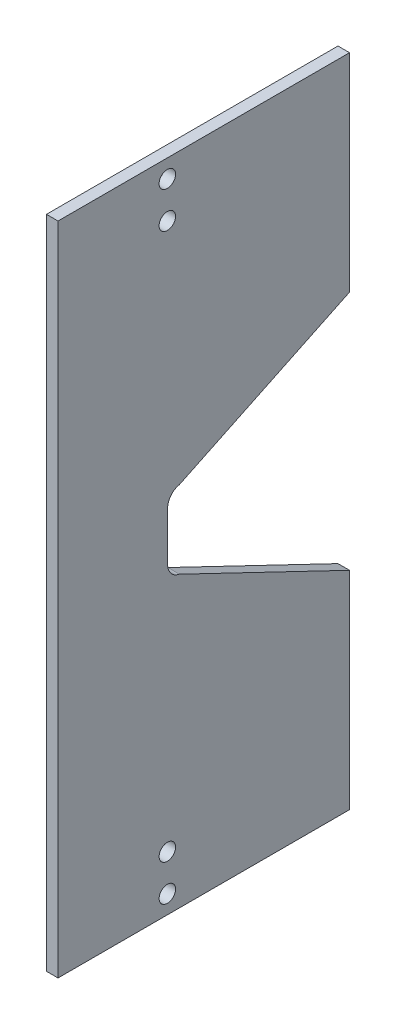
SolidWorks part; units mm, degrees
material "ABS"
ref_plane "前视基准面" through (0, 0, 0) normal (0, 0, 1) x (1, 0, 0)
ref_plane "上视基准面" through (0, 0, 0) normal (0, 1, 0) x (1, 0, 0)
ref_plane "右视基准面" through (0, 0, 0) normal (1, 0, 0) x (0, 0, -1)
ref_plane "基准面4" through (-0.7938, 0, 0) normal (-1, 0, 0) x (0, -1, 0)
sketch "草图1" plane through (-0.7938, 0, 0) normal (-1, 0, 0) x (0, -1, 0)
  line L1 (38.795, 5) -> (12.795, 5)
  line L2 (10.795, 3) -> (10.795, -13)
  line L5 (10.795, 3) -> (55.77, 3) construction
  line L6 (55.77, 3) -> (55.77, -5.0783) construction
  line L7 (55.77, 3) -> (55.77, 5) construction
  line L13 (38.795, 5) -> (72.745, 5)
  line L15 (100.745, 3) -> (100.745, -13)
  line L18 (72.745, 5) -> (98.745, 5)
  line L19 (55.77, 5) -> (55.77, -5.0783) construction
  line L20 (55.77, -5.0783) -> (55.77, -0.0391) construction
  line L21 (55.77, -0.0391) -> (65.77, -0.0391) construction
  line L22 (72.112, -14.1547) -> (62.1308, -0.0391) construction
  line L31 (12.795, -15) -> (47.795, -15)
  line L32 (55.77, -0.0391) -> (50.77, -0.0391)
  line L33 (55.77, -0.0391) -> (60.77, -0.0391)
  line L34 (98.745, -15) -> (63.745, -15)
  line L37 (50.77, -0.0391) -> (47.795, -15)
  line L38 (60.77, -0.0391) -> (63.745, -15)
  arc A2 (12.795, 5) -> (10.795, 3) centre (12.795, 3) ccw
  arc A3 (10.795, -13) -> (12.795, -15) centre (12.795, -13) ccw
  circle A5 centre (18.295, 0) radius 1.1303
  circle A6 centre (13.295, 0) radius 1.1303
  arc A12 (98.745, 5) -> (100.745, 3) centre (98.745, 3) cw
  arc A13 (100.745, -13) -> (98.745, -15) centre (98.745, -13) cw
  circle A14 centre (98.245, 0) radius 1.1303
  circle A15 centre (93.245, 0) radius 1.1303
extrude "凸台-拉伸1" add sketch "草图1" against normal blind 1.588
fillet "圆角1" radius 2 1 edges at (0.0002, -50.77, -0.0391)
fillet "圆角2" radius 2 1 edges at (0.0003, -47.795, -15)
fillet "圆角3" radius 2 1 edges at (0.0002, -60.77, -0.0391)
fillet "圆角4" radius 2 1 edges at (0.0003, -63.745, -15)
sketch "草图2" plane through (-0.7938, 0, 0) normal (-1, 0, 0) x (0, 0, 1)
  line L0 (5, -55.77) -> (15, -55.77) construction
  line L1 (5, -98.745) -> (5, -12.795) construction
  line L2 (15, -55.77) -> (15, -10.795) construction
  line L3 (15, -55.77) -> (15, -100.745) construction
  line L4 (15, -100.745) -> (3, -100.745) construction
  line L5 (3, -100.745) -> (3, -10.795) construction
  line L6 (3, -10.795) -> (15, -10.795) construction
  line L7 (3, -10.795) -> (15, -10.795)
  line L8 (15, -10.795) -> (15, -100.745)
  line L9 (15, -100.745) -> (3, -100.745)
  line L10 (3, -100.745) -> (3, -10.795)
  line L11 (-15, -29.4743) -> (-25, -29.4743) construction
  line L12 (-15, -12.795) -> (-15, -46.1535) construction
  line L13 (-25, -29.4743) -> (-25, -82.0657) construction
  line L14 (-25, -82.0657) -> (-25, -100.745) construction
  line L15 (-25, -100.745) -> (-13, -100.745) construction
  line L16 (-13, -100.745) -> (-13, -10.795) construction
  line L17 (-13, -10.795) -> (-25, -10.795) construction
  line L18 (-25, -10.795) -> (-25, -29.4743) construction
  line L19 (-1.6491, -50.4499) -> (-13.3901, -48.1151) construction
  line L20 (-13.3901, -48.1151) -> (-25, -45.8065) construction
  line L21 (-1.6491, -61.0901) -> (-13.3901, -63.4249) construction
  line L22 (-13.3901, -63.4249) -> (-25, -65.7335) construction
  line L23 (-25, -10.795) -> (-25, -45.8065)
  line L24 (-25, -45.8065) -> (-13.3901, -48.1151)
  line L26 (-13, -10.795) -> (-25, -10.795)
  line L27 (-13, -10.795) -> (-13.3901, -48.1151)
  line L28 (-13.3901, -63.4249) -> (-25, -65.7335)
  line L29 (-25, -65.7335) -> (-25, -100.745)
  line L30 (-25, -100.745) -> (-13, -100.745)
  line L31 (-13, -100.745) -> (-13.3901, -63.4249)
extrude "凸台-拉伸2" add sketch "草图2" against normal blind 1.588
sketch "草图5" plane through (0.7942, 0, 0) normal (1, 0, 0) x (0, 0, -1)
  line L0 (25, -10.795) -> (25, -45.8065) construction
  line L1 (25, -45.8065) -> (25, -28.3007) construction
  line L2 (25, -28.3007) -> (25, -37.0536) construction
  line L3 (25, -37.0536) -> (25, -45.8065) construction
  line L4 (25, -45.8065) -> (25, -41.43) construction
  line L5 (25, -41.43) -> (1.6491, -50.4499) construction
  line L6 (1.6491, -50.4499) -> (25, -45.8065)
  line L9 (0.0391, -55.77) -> (-15, -55.77) construction
  line L10 (0.0391, -52.4115) -> (0.0391, -59.1285) construction
  line L11 (-15, -100.745) -> (-15, -10.795) construction
  line L15 (25, -41.43) -> (25, -37.0536) construction
  line L16 (25, -37.0536) -> (25, -39.2418) construction
  line L17 (25, -39.2418) -> (1.6491, -50.4499) construction
  line L18 (1.6491, -50.4499) -> (25, -39.2418)
  line L19 (25, -39.2418) -> (25, -45.8065)
  line L20 (25, -72.2982) -> (25, -65.7335)
  line L21 (1.6491, -61.0901) -> (25, -65.7335)
  line L22 (1.6491, -61.0901) -> (25, -72.2982)
extrude "切除-拉伸1" cut sketch "草图5" against normal blind 10
